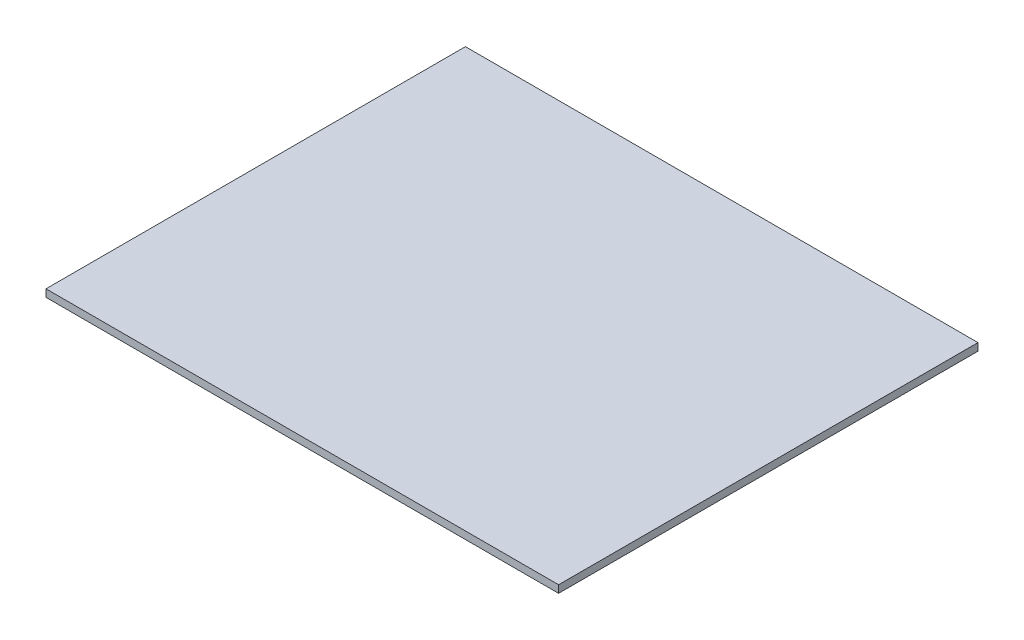
SolidWorks part; units mm, degrees
ref_plane "Front" through (0, 0, 0) normal (0, 0, 1) x (1, 0, 0)
ref_plane "Top" through (0, 0, 0) normal (0, 1, 0) x (1, 0, 0)
ref_plane "Right" through (0, 0, 0) normal (1, 0, 0) x (0, 0, -1)
sketch "Sketch1" plane through (0, 0, 0) normal (0, 1, 0) x (1, 0, 0)
  line L1 (0, 0) -> (110, 0)
  line L2 (0, 0) -> (0, 90)
  line L3 (0, 90) -> (110, 90)
  line L4 (110, 0) -> (110, 90)
  dimension "D1" = 110
  dimension "D2" = 90
extrude "Boss-Extrude1" add sketch "Sketch1" along normal blind 1.6
